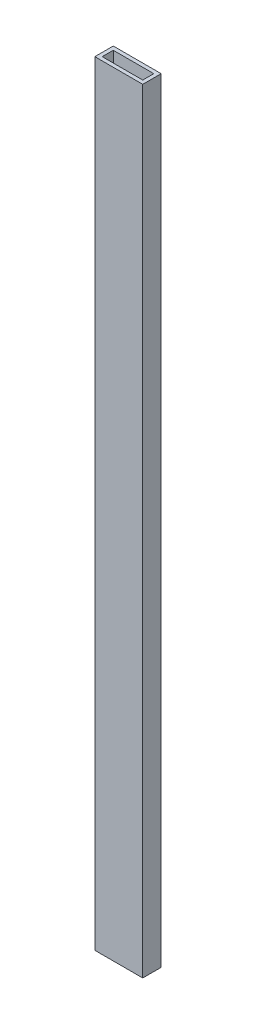
SolidWorks part; units mm, degrees
ref_plane "Front Plane" through (0, 0, 0) normal (0, 0, 1) x (1, 0, 0)
ref_plane "Top Plane" through (0, 0, 0) normal (0, 1, 0) x (1, 0, 0)
ref_plane "Right Plane" through (0, 0, 0) normal (1, 0, 0) x (0, 0, -1)
sketch "Sketch1" plane through (0, 0, 0) normal (0, 1, 0) x (1, 0, 0)
  line L0 (-20.6375, 7.9375) -> (-20.6375, -7.9375)
  line L1 (-17.4625, 4.7625) -> (17.4625, 4.7625)
  line L2 (-17.4625, 4.7625) -> (-17.4625, -4.7625)
  line L3 (-17.4625, -4.7625) -> (17.4625, -4.7625)
  line L4 (17.4625, 4.7625) -> (17.4625, -4.7625)
  line L5 (-17.4625, 4.7625) -> (17.4625, -4.7625) construction
  line L6 (-17.4625, -4.7625) -> (17.4625, 4.7625) construction
  line L7 (-20.6375, -7.9375) -> (20.6375, -7.9375)
  line L8 (20.6375, 7.9375) -> (20.6375, -7.9375)
  line L9 (-20.6375, 7.9375) -> (20.6375, 7.9375)
  point P0 (0, 0)
  dimension "D1" = 34.925
  dimension "D2" = 9.525
  dimension "D3" = 3.175
extrude "Boss-Extrude1" add sketch "Sketch1" along normal blind 666.75
